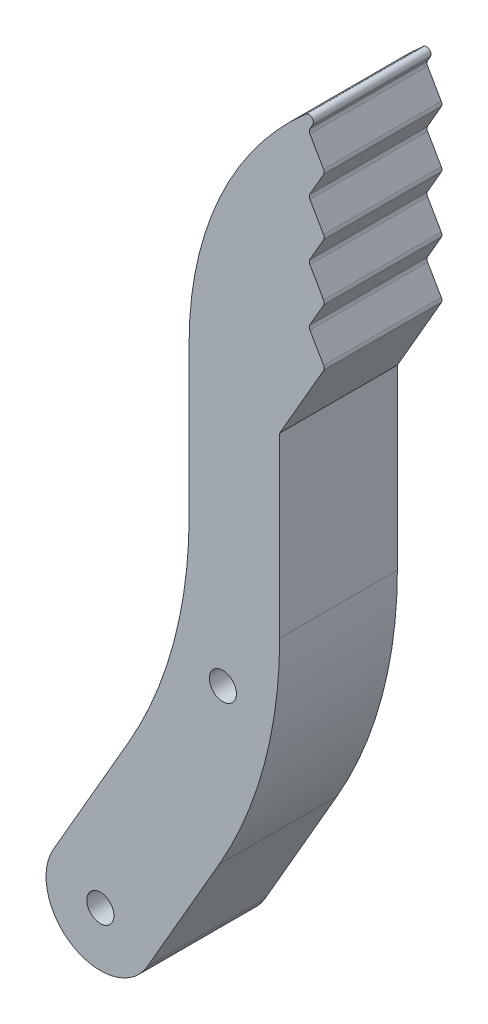
SolidWorks part; units mm, degrees
material "ABS"
ref_plane "Front Plane" through (0, 0, 0) normal (0, 0, 1) x (1, 0, 0)
ref_plane "Top Plane" through (0, 0, 0) normal (0, 1, 0) x (1, 0, 0)
ref_plane "Right Plane" through (0, 0, 0) normal (1, 0, 0) x (0, 0, -1)
sketch "Sketch1" plane through (0, 0, 0) normal (0, 0, 1) x (1, 0, 0)
  line L0 (0, 100) -> (0, -100) construction
  line L2 (0, 25) -> (-5, 16.3397)
  line L3 (-5, 16.3397) -> (-5, -3.282)
  line L5 (-11.6987, -28.282) -> (-19.6077, -41.9808)
  line L6 (-30, -35.9808) -> (-21.6987, -21.6025)
  line L7 (-15, 3.3975) -> (-15, 20)
  line L9 (0, 50) -> (-1.8042, 46.875)
  line L10 (-1.8042, 46.875) -> (0, 43.75)
  line L11 (0, 43.75) -> (-1.8042, 40.625)
  line L12 (-1.8042, 40.625) -> (0, 37.5)
  line L13 (0, 37.5) -> (-1.8042, 34.375)
  line L14 (-1.8042, 34.375) -> (0, 31.25)
  line L15 (0, 31.25) -> (-1.8042, 28.125)
  line L16 (-1.8042, 28.125) -> (0, 25)
  line L17 (-24.8038, -38.9808) -> (-11.5, -15.9378) construction
  line L18 (-16.7037, -9.5435) -> (-5.8481, -12.4522) construction
  line L19 (-15, 3.3975) -> (-5, -3.282) construction
  line L20 (-15.2506, -1.6025) -> (-5.2506, -8.282) construction
  arc A0 (-19.6077, -41.9808) -> (-30, -35.9808) centre (-24.8038, -38.9808) cw
  arc A1 (-15, 20) -> (0, 50) centre (22.5, 20) cw
  circle A2 centre (-24.8038, -38.9808) radius 1.5
  arc A5 (-21.6987, -21.6025) -> (-15, 3.3975) centre (-65, 3.3975) ccw
  arc A6 (-11.6987, -28.282) -> (-5, -3.282) centre (-55, -3.282) ccw
  circle A8 centre (-11.2759, -10.9979) radius 1.5
  circle A9 centre (-10.2506, -4.9423) radius 1.5 construction
  point P3 (0, 0)
  point P17 (0, 0)
  point P29 (-15, -10)
  point P32 (-27.8038, -44.1769)
  point P35 (-5, 16.3397)
  dimension "D5" = 60
  dimension "D6" = 30
  dimension "D8" = 10
  dimension "D9" = 30
  dimension "D11" = 6
  dimension "D13" = 50
  dimension "D16" = 3
  dimension "D4" = 50
  dimension "D17" = 3
  dimension "D14" = 50
  dimension "D23" = 3
  dimension "D1" = 25
  dimension "D2" = 150
  dimension "D3" = 10
  dimension "D7" = 120
  dimension "D10" = 30
  dimension "D12" = 200
  dimension "D18" = 6.5
  dimension "D19" = 150
  dimension "D20" = 94.1769
  dimension "D22" = 5
  dimension "D15" = 4
extrude "Boss-Extrude1" add sketch "Sketch1" along normal mid plane 13
fillet "Fillet1" radius 0.5 9 edges at (0, 25, 0) (0, 31.25, 0) (0, 37.5, 0) (0, 43.75, 0) (0, 50, 0) (-1.8042, 28.125, 0) (-1.8042, 34.375, 0) (-1.8042, 40.625, 0) (-1.8042, 46.875, 0)
